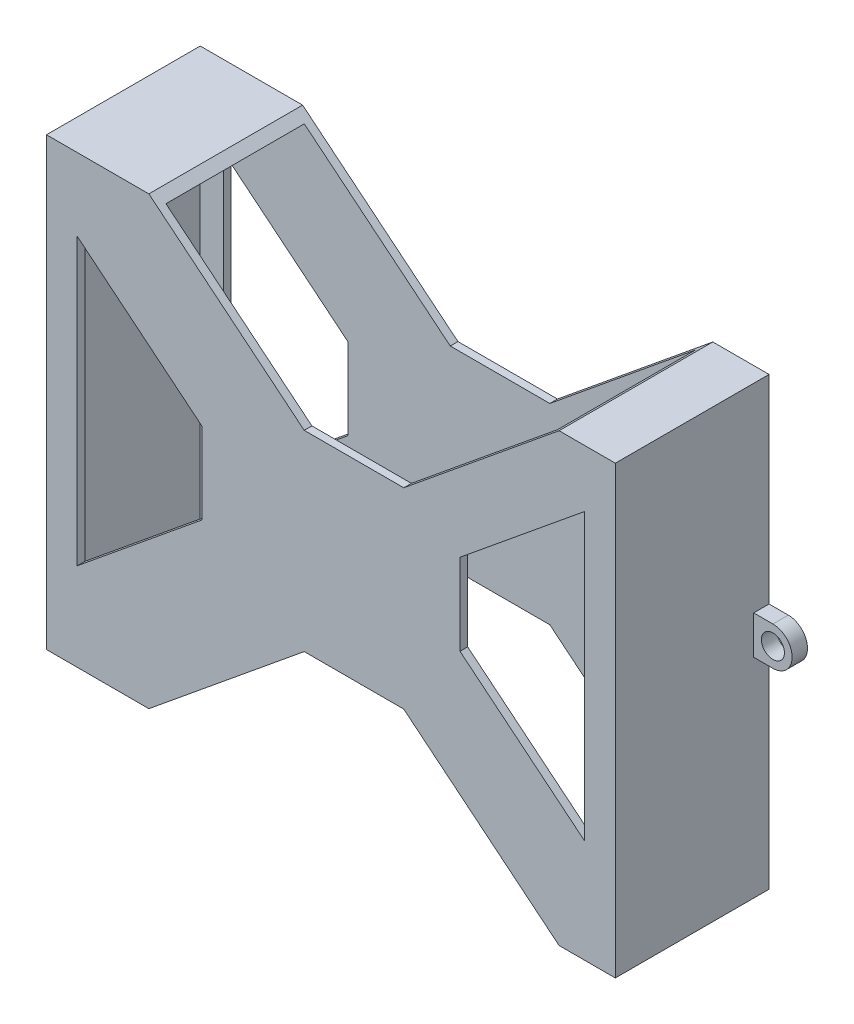
SolidWorks part; units mm, degrees
ref_plane "Ön Düzlem" through (0, 0, 0) normal (0, 0, 1) x (1, 0, 0)
ref_plane "Üst Düzlem" through (0, 0, 0) normal (0, 1, 0) x (1, 0, 0)
ref_plane "Sağ Düzlem" through (0, 0, 0) normal (1, 0, 0) x (0, 0, -1)
sketch "Sketch1" plane through (0, 0, 0) normal (0, 0, 1) x (1, 0, 0)
  line L0 (-23.6833, 29) -> (-3.4741, 12.4652)
  line L1 (-23.6833, 29) -> (29.6833, 29)
  line L3 (-23.6833, -29) -> (29.6833, -29)
  line L6 (33, 21.559) -> (33, -15.559)
  line L7 (-3.4741, 12.4652) -> (9.4741, 12.4652)
  line L8 (-16.7908, 6.297) -> (-16.7908, -4.297)
  line L9 (-3.4741, -12.4652) -> (9.4741, -12.4652)
  line L10 (16.7908, 8.297) -> (16.7908, -2.297)
  line L12 (-33, 19.559) -> (-33, -17.559)
  line L13 (-33, 19.559) -> (-16.7908, 6.297)
  line L14 (-33, -17.559) -> (-16.7908, -4.297)
  line L15 (-23.6833, -29) -> (-3.4741, -12.4652)
  line L17 (37, 29) -> (37, -29) construction
  line L18 (-37, 29) -> (37, 29) construction
  line L19 (-33, 25) -> (33, 25) construction
  line L20 (-33, 25) -> (-33, -25) construction
  line L21 (33, 25) -> (33, -25) construction
  line L22 (9.4741, -12.4652) -> (29.6833, -29)
  line L23 (-37, 29) -> (-37, -29) construction
  line L24 (16.7908, -2.297) -> (33, -15.559)
  line L25 (16.7908, 8.297) -> (33, 21.559)
  line L26 (-37, -29) -> (37, -29) construction
  line L27 (9.4741, 12.4652) -> (29.6833, 29)
  line L28 (-33, -25) -> (33, -25) construction
  line L30 (-37, 29) -> (37, 29)
  line L31 (-37, 29) -> (-37, -29)
  line L32 (-37, -29) -> (37, -29)
  line L33 (37, 29) -> (37, -29)
  line L34 (-37, 29) -> (37, -29) construction
  line L35 (-37, -29) -> (37, 29) construction
  point P0 (0, 0)
  point P6 (0, 0)
  point P13 (4.1888, 1.6685)
  point P14 (0, 0)
  point P16 (-4.8194, -3.9432)
  dimension "D1" = 4
  dimension "D2" = 74
  dimension "D3" = 4
  dimension "D4" = 4
  dimension "56" = 58
extrude "Boss-Extrude2" add sketch "Sketch1" along normal blind 20 contours L33 L30 L27 L7 L0 L31 L32 L15 L9 L22 L14 L12 L13 L8 L10 L25 L6 L24
shell "Shell2" thickness 1
sketch "Sketch2" plane through (0, 0, 0) normal (0, 0, 1) x (1, 0, 0)
  line L0 (-37, 29) -> (-37, -29) construction
  line L1 (-39.5, -1.8657) -> (-37, -1.8657)
  line L2 (-39.5, 3.1343) -> (-37, 3.1343)
  line L3 (-37, -1.8657) -> (-37, 3.1343)
  line L7 (37, 29) -> (37, -29) construction
  line L8 (39.5, 3.1343) -> (37, 3.1343)
  line L9 (39.5, -1.8657) -> (37, -1.8657)
  line L10 (37, -1.8657) -> (37, 3.1343)
  arc A0 (-39.5, 3.1343) -> (-39.5, -1.8657) centre (-39.5, 0.6343) ccw
  circle A1 centre (-39.5, 0.6343) radius 1.5
  circle A3 centre (39.5, 0.6343) radius 1.5
  arc A4 (39.5, -1.8657) -> (39.5, 3.1343) centre (39.5, 0.6343) ccw
  dimension "D1" = 2.5
  dimension "D3" = 3
  dimension "D2" = 2.5
extrude "Boss-Extrude4" add sketch "Sketch2" along normal blind 2
